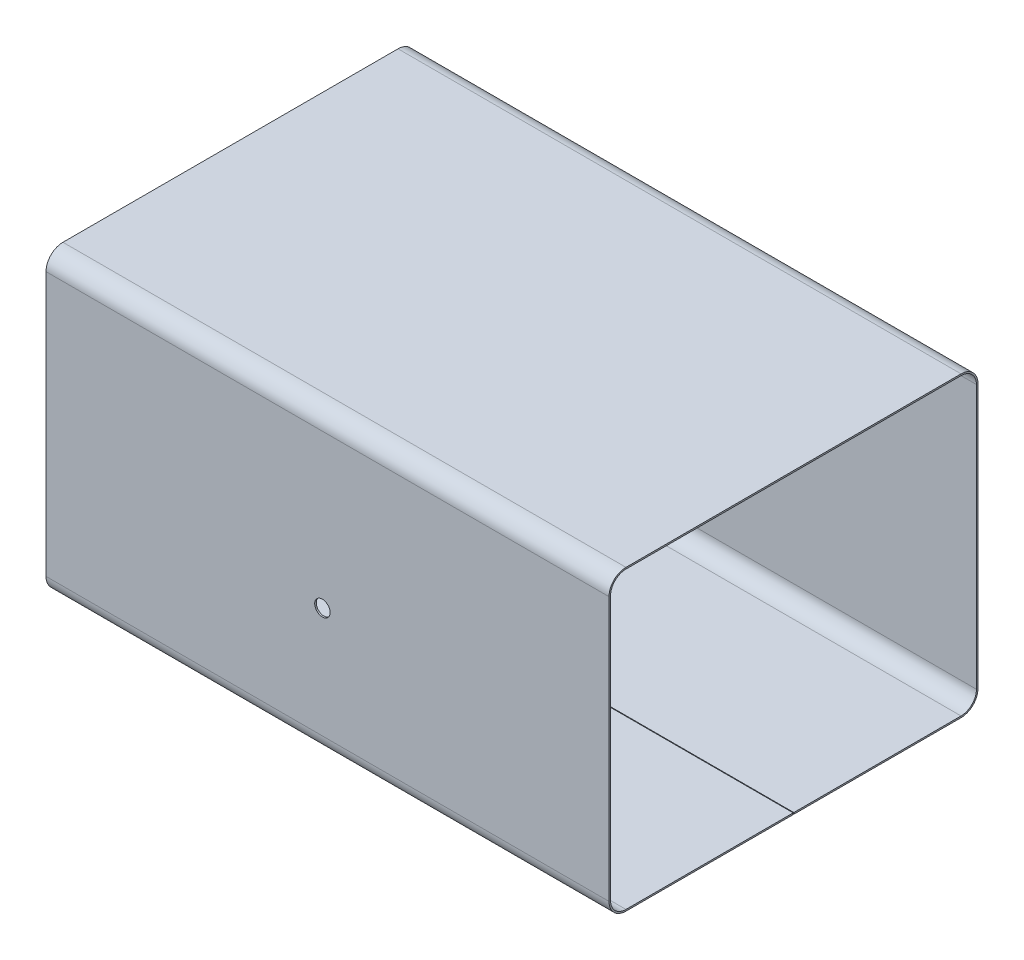
SolidWorks part; units mm, degrees
ref_plane "Front" through (0, 0, 0) normal (0, 0, 1) x (1, 0, 0)
ref_plane "Top" through (0, 0, 0) normal (0, 1, 0) x (1, 0, 0)
ref_plane "Right" through (0, 0, 0) normal (1, 0, 0) x (0, 0, -1)
sketch "Sketch1" plane through (0, 0, 0) normal (1, 0, 0) x (0, 0, -1)
  line L0 (0, 0) -> (0, -22.2691) construction
  line L1 (-54.3692, -47.8186) -> (-0.1, -47.8186)
  line L2 (-59.3692, -42.8186) -> (-59.3692, 42.8186)
  line L3 (-54.3692, 47.8186) -> (54.3692, 47.8186)
  line L4 (59.3692, -42.8186) -> (59.3692, 42.8186)
  line L5 (-59.3692, -47.8186) -> (59.3692, 47.8186) construction
  line L6 (-59.3692, 47.8186) -> (59.3692, -47.8186) construction
  line L7 (0.1, -47.8186) -> (54.3692, -47.8186)
  line L8 (-0.1, -22.4348) -> (0.1, -22.4348) construction
  line L9 (-0.1, -22.4348) -> (-0.1, -22.1035) construction
  line L10 (-0.1, -22.1035) -> (0.1, -22.1035) construction
  line L11 (0.1, -22.4348) -> (0.1, -22.1035) construction
  line L12 (-0.1, -22.4348) -> (0.1, -22.1035) construction
  line L13 (-0.1, -22.1035) -> (0.1, -22.4348) construction
  line L14 (-59.3692, 47.8186) -> (59.3692, 47.8186) construction
  line L15 (59.3692, 47.8186) -> (59.3692, -47.8186) construction
  line L16 (59.3692, -47.8186) -> (-59.3692, -47.8186) construction
  line L17 (-59.3692, -47.8186) -> (-59.3692, 47.8186) construction
  line L18 (-54.3692, 47.8186) -> (54.3692, 47.8186) construction
  line L19 (59.3692, -42.8186) -> (59.3692, 42.8186) construction
  arc A0 (59.3692, 42.8186) -> (54.3692, 47.8186) centre (54.3692, 42.8186) ccw
  arc A1 (59.3692, -42.8186) -> (54.3692, -47.8186) centre (54.3692, -42.8186) cw
  arc A2 (-59.3692, -42.8186) -> (-54.3692, -47.8186) centre (-54.3692, -42.8186) ccw
  arc A3 (-59.3692, 42.8186) -> (-54.3692, 47.8186) centre (-54.3692, 42.8186) cw
  point P0 (0, 0)
  dimension "D2" = 5
  dimension "D1" = 0.2
extrude "Extrude-Thin1" add sketch "Sketch1" against normal up to vertex (182.7 mm away) thin
sketch "Sketch2" plane through (0, 0, 59.8692) normal (0, 0, 1) x (1, 0, 0)
  line L0 (0, 0) -> (-182.7, 0) construction
  line L1 (0, 42.8186) -> (0, -42.8186) construction
  line L2 (-182.7, 42.8186) -> (-182.7, -42.8186) construction
  circle A0 centre (-93.0069, -6.8868) radius 2.5
  circle A1 centre (-93.0069, -6.8868) radius 2.5 construction
extrude "Cut-Extrude1" cut sketch "Sketch2" against normal through all
